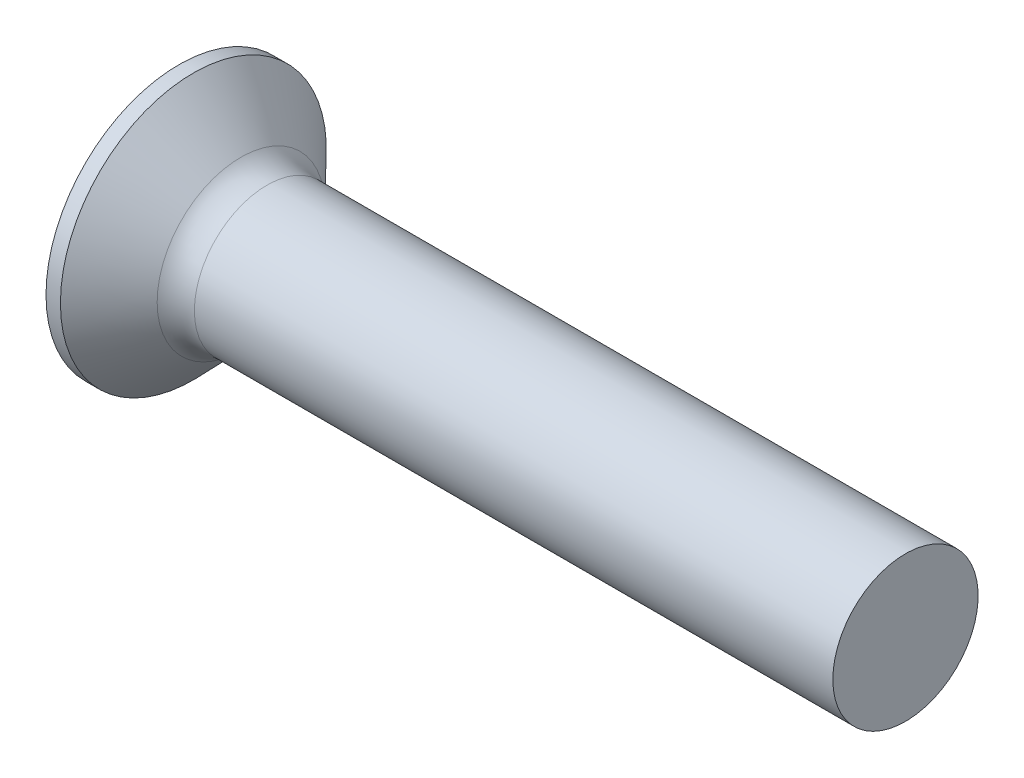
SolidWorks part; units mm, degrees
revolve "Base-Revolve" add sketch "BodySke" angle 360 about L5
sketch "BodySke" plane through (0, 0, 0) normal (0, 0, 1) x (1, 0, 0)
  line L0 (0, 0) -> (0, 9.15)
  line L1 (0, 9.15) -> (0.9924, 9.15)
  line L2 (5, 5) -> (50, 5)
  line L3 (50, 5) -> (50, 0)
  line L4 (50, 0) -> (0, 0)
  line L5 (-6.35, 0) -> (82.55, 0) construction
  line L6 (5, -5) -> (50, -5) construction
  line L7 (0.9924, -9.15) -> (5, -5) construction
  line L8 (0.9924, 9.15) -> (5, 5)
  line L9 (0, -9.15) -> (0.9924, -9.15) construction
  line L10 (6.5, 6.5875) -> (6.5, -2.9375) construction
  line L11 (0, 6.35) -> (0, -3.175) construction
cosmetic thread "ThreadCosmetic" [suppressed] parameters "Thread_length"=22.85, "Thread_minor"=7.9248
ref_plane "Plane1" through (0, 0, 0) normal (0, 0, 1) x (1, 0, 0)
ref_plane "Plane2" through (0, 0, 0) normal (0, 1, 0) x (1, 0, 0)
ref_plane "Plane3" through (0, 0, 0) normal (1, 0, 0) x (0, 0, -1)
other "Configuration Table"
fillet "Fillet1" radius 2.5 1 edges at (5, 0, 5)
sketch "Sketch3" plane through (0, 0, 0) normal (-1, 0, 0) x (0, 0, 1)
  line L0 (-1.08, 4.9) -> (1.08, 4.9)
  line L1 (1.08, 4.9) -> (1.08, -4.9)
  line L2 (1.08, -4.9) -> (-1.08, -4.9)
  line L3 (-1.08, -4.9) -> (-1.08, 4.9)
  dimension "D1" = 1.5
  dimension "D2" = 0.37
ref_plane "Plane4" through (5.64, 0, 0) normal (-1, 0, 0) x (0, 0, 1)
sketch "Sketch4" plane through (5.64, 0, 0) normal (-1, 0, 0) x (0, 0, 1)
  line L0 (-1.08, 2.088) -> (1.08, 2.088)
  line L3 (1.08, 2.088) -> (1.08, -2.088)
  line L4 (1.08, -2.088) -> (-1.08, -2.088)
  line L5 (-1.08, -2.088) -> (-1.08, 2.088)
  dimension "D2" = 0.9957
  dimension "D1" = 0.74
  dimension "D4" = 0.4979
  dimension "D3" = 0.37
loft "Recess" cut profiles "Sketch3", "Sketch4"
pattern_circular "RecPat" count 2 every 90 about axis through (0, 0, 0) along (1, 0, 0) of "Recess"
sketch "RecCorSke" plane through (0, 0, 0) normal (0, 0, 1) x (1, 0, 0)
  line L0 (-3.175, 0) -> (15.875, 0) construction
  line L2 (0, 0) -> (0, 2.3249)
  line L3 (0, 2.3249) -> (5.64, 1.9305)
  line L4 (5.64, 1.9305) -> (6.2673, 0)
  line L5 (6.2673, 0) -> (0, 0)
  dimension "Depth" = 2.01
  dimension "Draft_angle" = 4
  dimension "Bottom_angle" = 18
revolve "RecessCore" cut sketch "RecCorSke" angle 360 about L0
sketch "ThdSchSke" plane through (0, 0, 0) normal (0, 0, 1) x (1, 0, 0)
  line L0 (6.5, -3.9624) -> (5.7735, -5)
  line L1 (6.5, -3.9624) -> (7.2265, -5)
  line L2 (7.2265, -5) -> (7.2265, -6.25)
  line L3 (-3.175, 0) -> (5.1513, 0) construction
  line L5 (7.2265, -6.25) -> (5.7735, -6.25)
  line L6 (5.7735, -6.25) -> (5.7735, -5)
  line L7 (0, 9.15) -> (0, -9.15) construction
  dimension "Thread_minor" = 2.439
  dimension "Diameter" = 3
  dimension "Start" = 2.15
revolve "ThreadSchematic" [suppressed] cut sketch "ThdSchSke" angle 360 about L3
pattern_linear "ThdSchPat" [suppressed]
equation "\"D1@Sketch3\" = \"Cross_dia@Sketch3\" / 2"
equation "\"D2@Sketch3\" = \"Cross_width@Sketch3\" / 2"
equation "\"Depth@RecCorSke\" = \"Cross_depth@Plane4\""
equation "\"D1@Sketch4\" = \"Cross_width@Sketch3\""
equation "\"D2@Sketch4\" = \"Cross_dia@Sketch3\" - 2.0 * \"Cross_depth@Plane4\" * tan(26.5  * 0.017453292)"
equation "\"D3@Sketch4\" = \"D1@Sketch4\" / 2"
equation "\"D4@Sketch4\" = \"D2@Sketch4\" / 2"
equation "\"Thread_length@ThreadCosmetic\" = ((sgn( (\"Length@BodySke\" - \"Advance@BodySke\" * 1.0 - \"Head_ht@BodySke\" ) - \"Thread_nom@BodySke\" )-1)*( (\"Length@BodySke\" - \"Advance@BodySke\" * 1.0 - \"Head_ht@BodySke\" ) - \"Thread_nom@BodySke\" ))/-2+ \"Thread_nom@BodySke\""
equation "\"Thread_minor@ThdSchSke\" = \"Thread_minor@ThreadCosmetic\""
equation "\"Diameter@ThdSchSke\" = \"Diameter@BodySke\""
equation "\"Overcut@ThdSchSke\" = \"Diameter@BodySke\" * 1.25"
equation "\"Start@ThdSchSke\" = 0.000001 + \"Length@BodySke\" - \"Thread_length@ThreadCosmetic\"  '---Countersunk---"
equation "\"Num_threads@ThdSchPat\" = int( \"Thread_length@ThreadCosmetic\" / \"Advance@BodySke\" + 0.999 )  + 1"
equation "\"Advance@ThdSchPat\" = \"Thread_length@ThreadCosmetic\" /  (\"Num_threads@ThdSchPat\" - 1) 'relax it"
